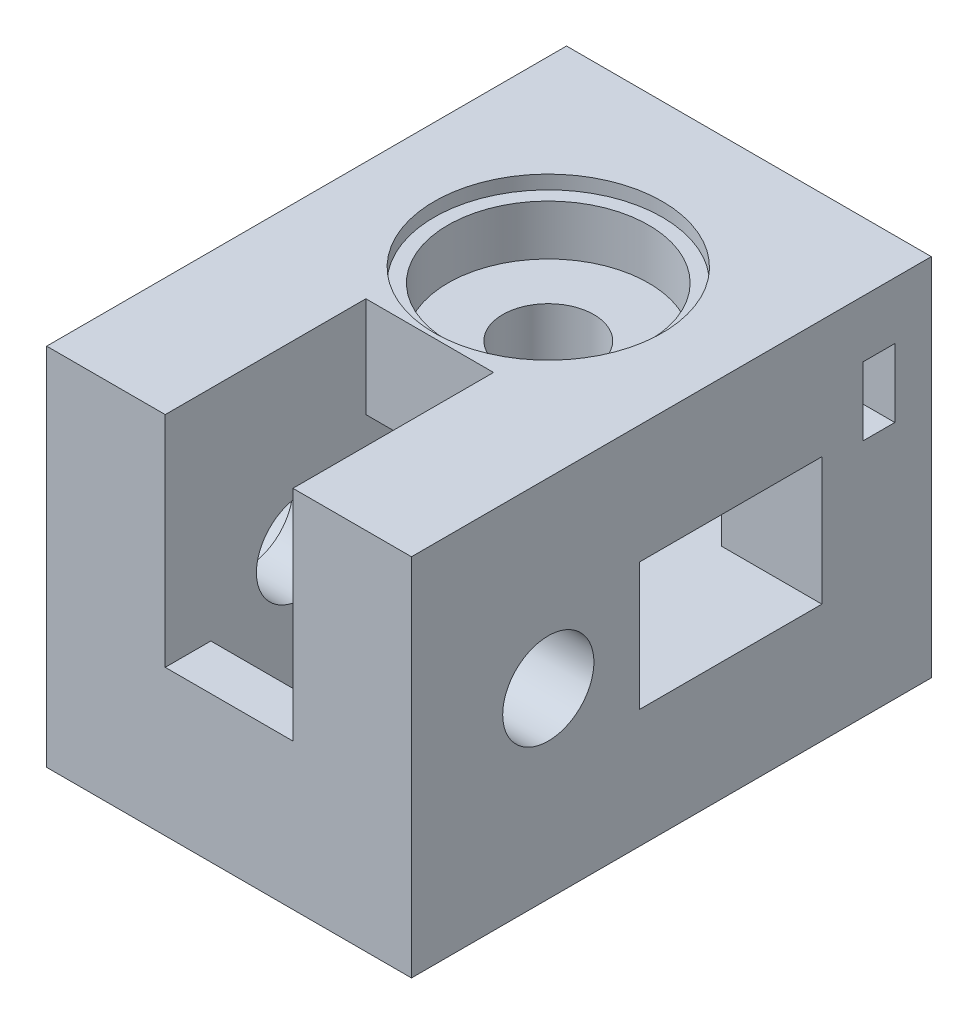
SolidWorks part; units mm, degrees
ref_plane "Plan de face" through (0, 0, 0) normal (0, 0, 1) x (1, 0, 0)
ref_plane "Plan de dessus" through (0, 0, 0) normal (0, 1, 0) x (1, 0, 0)
ref_plane "Plan de droite" through (0, 0, 0) normal (1, 0, 0) x (0, 0, -1)
sketch "Esquisse1" plane through (0, 0, 0) normal (0, 0, 1) x (1, 0, 0)
  line L1 (-40, 40) -> (0, 40)
  line L2 (-40, 40) -> (-40, 0)
  line L3 (-40, 0) -> (0, 0)
  line L4 (0, 40) -> (0, 0)
  dimension "D1" = 40
  dimension "D2" = 40
extrude "Boss.-Extru.1" add sketch "Esquisse1" along normal blind 50
sketch "Esquisse2" plane through (0, 40, 0) normal (0, 1, 0) x (1, 0, 0)
  line L0 (0, 0) -> (-40, 0) construction
  line L1 (-40, -50) -> (-40, 0) construction
  circle A0 centre (-20, -15) radius 5
  dimension "D1" = 10
  dimension "D2" = 15
  dimension "D3" = 20
extrude "Enlèv. mat.-Extru.1" cut sketch "Esquisse2" against normal through all
sketch "Esquisse3" plane through (-40, 0, 0) normal (-1, 0, 0) x (0, 0, 1)
  line L0 (50, 40) -> (50, 0) construction
  line L1 (50, 40) -> (0, 40) construction
  circle A0 centre (35, 20) radius 5
  dimension "D1" = 10
  dimension "D2" = 15
  dimension "D3" = 20
extrude "Enlèv. mat.-Extru.2" cut sketch "Esquisse3" against normal through all
sketch "Esquisse4" plane through (-40, 0, 0) normal (-1, 0, 0) x (0, 0, 1)
  line L1 (22, 27) -> (0, 27)
  line L2 (22, 27) -> (22, 13)
  line L3 (22, 13) -> (0, 13)
  line L4 (0, 27) -> (0, 13)
  line L5 (0, 40) -> (0, 0) construction
  line L6 (50, 0) -> (0, 0) construction
  line L7 (50, 40) -> (0, 40) construction
  dimension "D1" = 14
  dimension "D2" = 22
  dimension "D3" = 0
  dimension "D4" = 13
  dimension "D5" = 13
extrude "Enlèv. mat.-Extru.3" cut sketch "Esquisse4" against normal blind 29
sketch "Esquisse5" plane through (0, 0, 0) normal (0, -1, 0) x (1, 0, 0)
  line L0 (-40, 50) -> (0, 50) construction
  line L1 (-13, 25) -> (-27, 25)
  line L2 (-13, 25) -> (-13, 45)
  line L3 (-13, 45) -> (-27, 45)
  line L4 (-27, 25) -> (-27, 45)
  line L5 (-40, 50) -> (-40, 0) construction
  dimension "D1" = 20
  dimension "D2" = 5
  dimension "D3" = 14
  dimension "D4" = 13
extrude "Enlèv. mat.-Extru.4" cut sketch "Esquisse5" against normal blind 29
sketch "Esquisse6" plane through (0, 0, 0) normal (1, 0, 0) x (0, 0, -1)
  line L1 (-5, 27) -> (-25, 27)
  line L2 (0, 0) -> (0, 40) construction
  line L3 (-5, 13) -> (-25, 13)
  line L4 (-25, 27) -> (-25, 13)
  line L5 (-50, 0) -> (0, 0) construction
  line L6 (-5, 27) -> (-5, 13)
  dimension "D1" = 14
  dimension "D2" = 5
  dimension "D3" = 13
  dimension "D4" = 20
extrude "Enlèv. mat.-Extru.5" cut sketch "Esquisse6" against normal blind 24
sketch "Esquisse7" plane through (0, 40, 0) normal (0, 1, 0) x (1, 0, 0)
  line L0 (0, -50) -> (-40, -50) construction
  line L1 (-27, -50) -> (-13, -50)
  line L2 (-27, -50) -> (-27, -28)
  line L3 (-27, -28) -> (-13, -28)
  line L4 (-13, -50) -> (-13, -28)
  line L5 (-40, -50) -> (-40, 0) construction
  dimension "D1" = 14
  dimension "D2" = 22
  dimension "D3" = 13
extrude "Enlèv. mat.-Extru.6" cut sketch "Esquisse7" against normal blind 24
sketch "Esquisse10" plane through (0, 40, 0) normal (0, 1, 0) x (1, 0, 0)
  circle A0 centre (-20, -15) radius 11
  dimension "D1" = 22
extrude "Enlèv. mat.-Extru.9" cut sketch "Esquisse10" against normal blind 7
sketch "Esquisse11" plane through (0, 40, 0) normal (0, 1, 0) x (1, 0, 0)
  circle A0 centre (-20, -15) radius 12.5
  dimension "D1" = 25
extrude "Enlèv. mat.-Extru.10" cut sketch "Esquisse11" against normal blind 1.5
sketch "Esquisse14" plane through (-40, 0, 0) normal (-1, 0, 0) x (0, 0, 1)
  circle A0 centre (35, 20) radius 11
  dimension "D1" = 22
extrude "Enlèv. mat.-Extru.11" cut sketch "Esquisse14" against normal blind 7
sketch "Esquisse15" plane through (-40, 0, 0) normal (-1, 0, 0) x (0, 0, 1)
  circle A0 centre (35, 20) radius 12.5
  dimension "D1" = 25
extrude "Enlèv. mat.-Extru.12" cut sketch "Esquisse15" against normal blind 1.5
sketch "Esquisse16" plane through (0, 0, 0) normal (0, 0, -1) x (-1, 0, 0)
  line L1 (0, 40) -> (40, 40)
  line L2 (0, 40) -> (0, 0)
  line L3 (0, 0) -> (40, 0)
  line L4 (40, 40) -> (40, 0)
extrude "Boss.-Extru.2" add sketch "Esquisse16" along normal blind 7
sketch "Esquisse17" plane through (0, 0, -7) normal (0, 0, -1) x (-1, 0, 0)
  line L0 (40, 40) -> (0, 40) construction
  line L1 (40, 0) -> (40, 40) construction
  circle A0 centre (7.5, 30) radius 2.25
  circle A1 centre (30, 7.5) radius 2.25
  dimension "D1" = 4.5
  dimension "D2" = 4.5
  dimension "D3" = 32.5
  dimension "D4" = 32.5
  dimension "D5" = 10
  dimension "D6" = 10
extrude "Enlèv. mat.-Extru.13" cut sketch "Esquisse17" against normal blind 15
sketch "Esquisse18" plane through (0, 0, 0) normal (1, 0, 0) x (0, 0, -1)
  line L0 (7, 40) -> (7, 0) construction
  line L1 (3, 33.75) -> (-0.5, 33.75)
  line L2 (3, 33.75) -> (3, 26.25)
  line L3 (3, 26.25) -> (-0.5, 26.25)
  line L4 (-0.5, 33.75) -> (-0.5, 26.25)
  line L9 (-50, 40) -> (7, 40) construction
  dimension "D1" = 7.5
  dimension "D2" = 3.5
  dimension "D3" = 4
  dimension "D4" = 6.25
extrude "Enlèv. mat.-Extru.14" cut sketch "Esquisse18" against normal blind 12
sketch "Esquisse19" plane through (0, 0, 0) normal (0, -1, 0) x (1, 0, 0)
  line L0 (0, -7) -> (-40, -7) construction
  line L1 (-26.25, -3) -> (-33.75, -3)
  line L2 (-26.25, -3) -> (-26.25, 0.5)
  line L3 (-26.25, 0.5) -> (-33.75, 0.5)
  line L4 (-33.75, -3) -> (-33.75, 0.5)
  line L5 (-40, 50) -> (-40, -7) construction
  dimension "D1" = 7.5
  dimension "D2" = 3.5
  dimension "D3" = 4
  dimension "D4" = 6.25
extrude "Enlèv. mat.-Extru.15" cut sketch "Esquisse19" against normal blind 12
